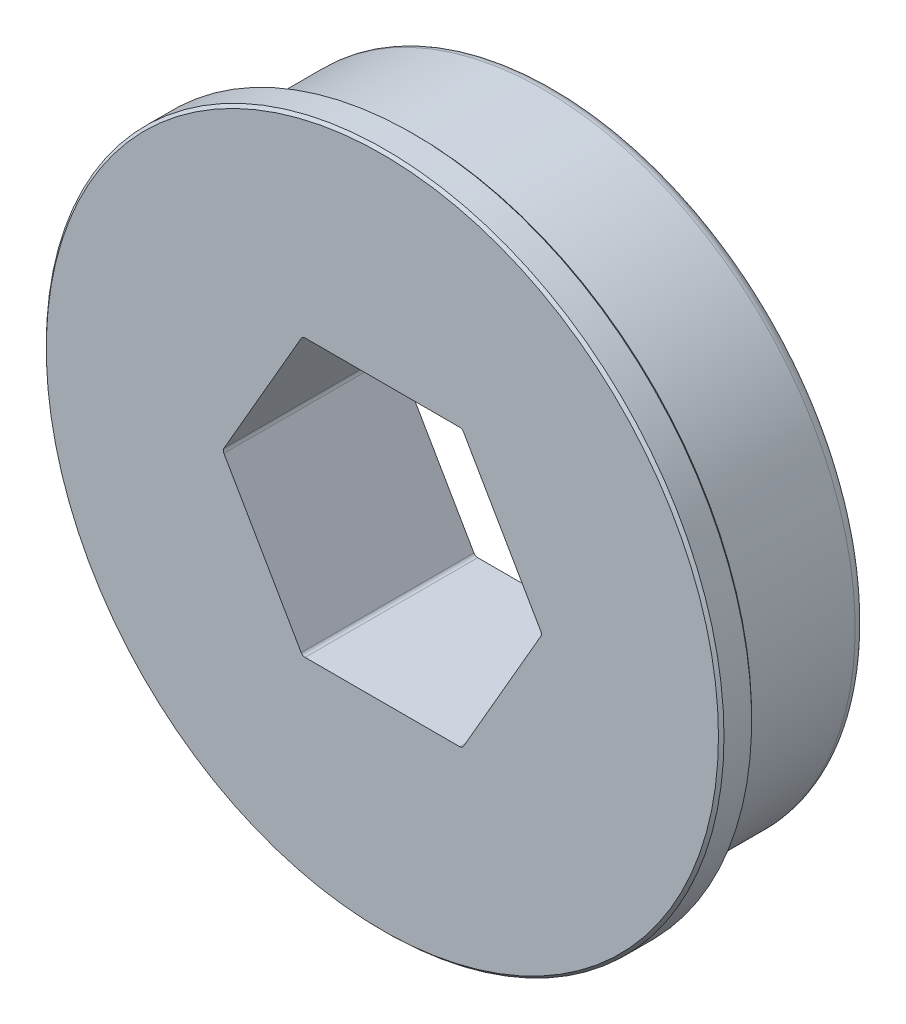
SolidWorks part; units mm, degrees
material "1023 Carbon Steel Sheet (SS)"
ref_plane "Front Plane" through (0, 0, 0) normal (0, 0, 1) x (1, 0, 0)
ref_plane "Top Plane" through (0, 0, 0) normal (0, 1, 0) x (1, 0, 0)
ref_plane "Right Plane" through (0, 0, 0) normal (1, 0, 0) x (0, 0, -1)
ref_plane "Plane1" through (0, 0, 0) normal (0, -1, 0) x (1, 0, 0)
sketch "Sketch1" plane through (0, 0, 0) normal (0, -1, 0) x (1, 0, 0)
  line L0 (15.5575, 7.9273) -> (0, 7.9273)
  line L1 (0, 7.9273) -> (0, 0)
  line L2 (0, 0) -> (14.2875, 0)
  line L3 (14.2875, 0) -> (14.2875, 5.8953)
  line L4 (14.2875, 5.8953) -> (13.97, 5.8953)
  line L5 (13.97, 5.8953) -> (13.97, 6.4033)
  line L6 (13.97, 6.4033) -> (15.5575, 6.4033)
  line L7 (15.5575, 6.4033) -> (15.5575, 7.9273)
  line L8 (0, 7.9273) -> (0, 0) construction
revolve "Revolve1" add sketch "Sketch1" angle 360 about L8
sketch "Sketch2" plane through (0, 0, 0) normal (0, 0, -1) x (-1, 0, 0)
  line L0 (3.6662, 6.35) -> (-3.6662, 6.35)
  line L1 (-3.6662, 6.35) -> (-7.3323, 0)
  line L2 (-7.3323, 0) -> (-3.6662, -6.35)
  line L3 (-3.6662, -6.35) -> (3.6662, -6.35)
  line L4 (3.6662, -6.35) -> (7.3323, 0)
  line L5 (7.3323, 0) -> (3.6662, 6.35)
  line L6 (3.6662, 6.35) -> (-3.6662, -6.35) construction
  line L8 (-3.8862, -6.7311) -> (-3.6662, -6.35) construction
  circle A0 centre (0, 0) radius 6.35 construction
  circle A1 centre (0, 0) radius 7.7724 construction
  dimension "D1" = 12.7
  dimension "D2" = 15.5448
  dimension "D3" = 0.4401
extrude "Cut-Extrude1" cut sketch "Sketch2" against normal through all
chamfer "Chamfer1" distance 0.127 angle 45 1 edges at (-15.5575, 0, 6.4033)
chamfer "Chamfer2" distance 0.127 angle 45 1 edges at (-15.5575, 0, 7.9273)
fillet "Fillet1" radius 0.508 1 edges at (-14.2875, 0, 0)
fillet "Fillet2" radius 0.2032 6 edges at (3.6662, 6.35, 3.9637) (7.3323, 0, 3.9637) (3.6662, -6.35, 3.9637) (-3.6662, -6.35, 3.9637) (-7.3323, 0, 3.9637) (-3.6662, 6.35, 3.9637)
